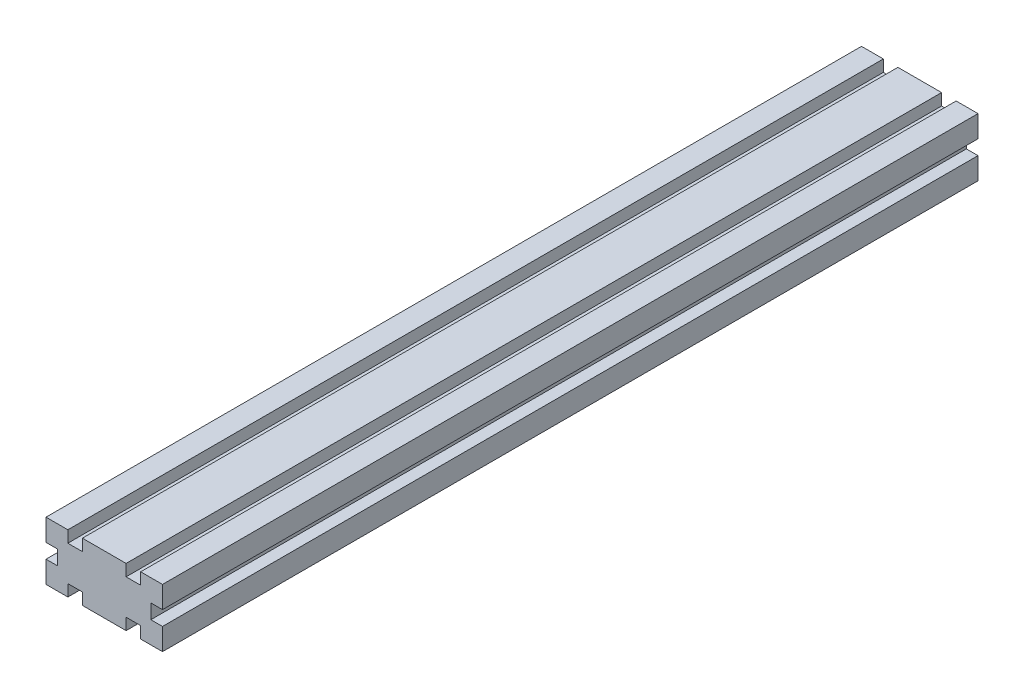
SolidWorks part; units mm, degrees
ref_plane "Plan de face" through (0, 0, 0) normal (0, 0, 1) x (1, 0, 0)
ref_plane "Plan de dessus" through (0, 0, 0) normal (0, 1, 0) x (1, 0, 0)
ref_plane "Plan de droite" through (0, 0, 0) normal (1, 0, 0) x (0, 0, -1)
sketch "Esquisse1" plane through (0, 0, 0) normal (0, 0, 1) x (1, 0, 0)
  line L0 (20, 20) -> (20, 0)
  line L1 (0, 0) -> (40, 0)
  line L2 (0, 0) -> (0, 20)
  line L3 (0, 20) -> (40, 20)
  line L4 (40, 0) -> (40, 20)
  line L5 (20, 0) -> (40, 20)
  line L6 (40, 0) -> (20, 20)
  line L7 (0, 0) -> (20, 20)
  line L8 (20, 0) -> (0, 20)
  line L10 (4, 4) -> (16, 4)
  line L11 (4, 4) -> (4, 16)
  line L12 (4, 16) -> (16, 16)
  line L13 (16, 4) -> (16, 16)
  line L14 (4, 4) -> (16, 16) construction
  line L15 (4, 16) -> (16, 4) construction
  line L16 (24, 4) -> (36, 4)
  line L17 (24, 4) -> (24, 16)
  line L18 (24, 16) -> (36, 16)
  line L19 (36, 4) -> (36, 16)
  line L20 (24, 4) -> (36, 16) construction
  line L21 (24, 16) -> (36, 4) construction
  line L22 (12.5, 0) -> (7.5, 0)
  line L23 (12.5, 0) -> (12.5, 20)
  line L24 (12.5, 20) -> (7.5, 20)
  line L25 (7.5, 0) -> (7.5, 20)
  line L26 (12.5, 0) -> (7.5, 20) construction
  line L27 (12.5, 20) -> (7.5, 0) construction
  line L28 (32.5, 0) -> (27.5, 0)
  line L29 (32.5, 0) -> (32.5, 20)
  line L30 (32.5, 20) -> (27.5, 20)
  line L31 (27.5, 0) -> (27.5, 20)
  line L32 (32.5, 0) -> (27.5, 20) construction
  line L33 (32.5, 20) -> (27.5, 0) construction
  line L34 (0, 7.5) -> (40, 7.5)
  line L35 (0, 7.5) -> (0, 12.5)
  line L36 (0, 12.5) -> (40, 12.5)
  line L37 (40, 7.5) -> (40, 12.5)
  line L38 (0, 7.5) -> (40, 12.5) construction
  line L39 (0, 12.5) -> (40, 7.5) construction
  point P7 (10, 10)
  point P12 (30, 10)
  point P17 (10, 10)
  point P22 (30, 10)
  point P27 (20, 10)
  dimension "D1" = 20
  dimension "D2" = 40
  dimension "D3" = 12
  dimension "D5" = 5
  dimension "D6" = 5
  dimension "D7" = 5
extrude "Boss.-Extru.1" add sketch "Esquisse1" along normal blind 280 contours L12 L25 L3 L8 | L2 L36 L11 L8 | L34 L2 L7 L11 | L1 L25 L10 L7 | L34 L11 L7 | L10 L25 L7 | L11 L36 L8 | L8 L25 L12 | L36 L11 L34 L25 | L25 L7 L8 | L36 L8 L7 | L8 L23 L7 | L7 L34 L8 | L23 L10 L8 | L34 L8 L13 | L34 L13 L8 L0 | L25 L36 L23 L12 | L36 L23 L34 L13 | L23 L7 L12 | L23 L12 L7 L3 | L7 L36 L13 | L13 L36 L0 L7 | L23 L1 L8 L10 | L34 L25 L10 L23 | L36 L13 L34 L0 | L36 L0 L34 L17 | L0 L36 L17 L6 | L18 L31 L3 L6 | L17 L36 L6 | L6 L31 L18 | L36 L17 L34 L31 | L34 L17 L5 | L34 L0 L5 L17 | L1 L31 L16 L5 | L16 L31 L5 | L34 L31 L16 L29 | L29 L16 L6 | L34 L6 L19 | L34 L19 L6 L4 | L29 L1 L6 L16 | L36 L29 L34 L19 | L6 L29 L5 | L5 L34 L6 | L31 L5 L6 | L36 L6 L5 | L5 L36 L19 | L29 L5 L18 | L29 L18 L5 L3 | L19 L36 L4 L5 | L31 L36 L29 L18
